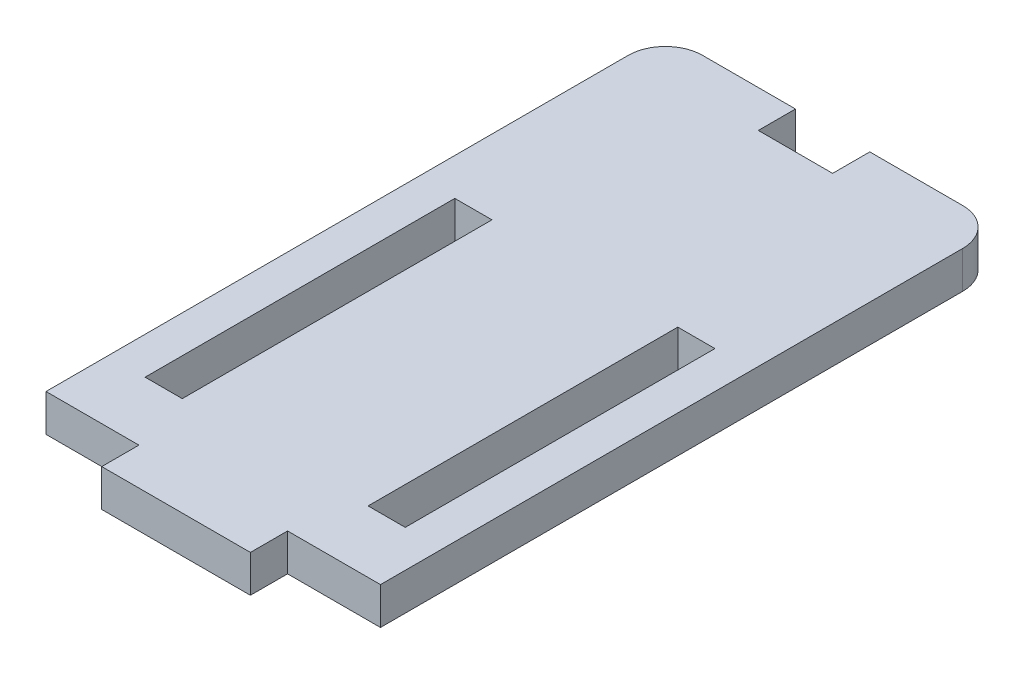
SolidWorks part; units mm, degrees
material "Acrylic (Medium-high impact)"
ref_plane "Plano frontal" through (0, 0, 0) normal (0, 0, 1) x (1, 0, 0)
ref_plane "Plano superior" through (0, 0, 0) normal (0, 1, 0) x (1, 0, 0)
ref_plane "Plano direito" through (0, 0, 0) normal (1, 0, 0) x (0, 0, -1)
sketch "Sketch1" plane through (0, 0, 0) normal (0, 1, 0) x (1, 0, 0)
  line L1 (-13.5, 25) -> (13.5, 25)
  line L2 (-13.5, 25) -> (-13.5, -25)
  line L3 (-13.5, -25) -> (13.5, -25)
  line L4 (13.5, 25) -> (13.5, -25)
  point P4 (-13.5, 0)
  point P6 (0, 25)
  dimension "D1" = 50
  dimension "D2" = 27
extrude "Boss-Extrude1" add sketch "Sketch1" along normal mid plane 3
sketch "Sketch2" plane through (0, 0, 0) normal (0, 1, 0) x (1, 0, 0)
  line L0 (-13.5, -25) -> (13.5, -25) construction
  line L1 (-6, -25) -> (6, -25)
  line L2 (-6, -25) -> (-6, -28)
  line L3 (-6, -28) -> (6, -28)
  line L4 (6, -25) -> (6, -28)
  line L5 (-13.5, 25) -> (-13.5, -25) construction
  point P6 (0, -28)
  dimension "D1" = 3
  dimension "D2" = 12
  dimension "D3" = 7.5
extrude "Boss-Extrude2" add sketch "Sketch2" along normal mid plane 3
sketch "Sketch4" plane through (0, 0, 0) normal (0, 1, 0) x (1, 0, 0)
  line L0 (-13.5, 25) -> (-13.5, -25) construction
  line L1 (-10.5, 5) -> (-7.5, 5)
  line L2 (-10.5, 5) -> (-10.5, -20)
  line L3 (-10.5, -20) -> (-7.5, -20)
  line L4 (-7.5, 5) -> (-7.5, -20)
  line L5 (0, -1.65) -> (0, 1.65) construction
  line L6 (7.5, 5) -> (7.5, -20)
  line L7 (10.5, -20) -> (7.5, -20)
  line L8 (10.5, 5) -> (10.5, -20)
  line L9 (10.5, 5) -> (7.5, 5)
  line L10 (13.5, 25) -> (-13.5, 25) construction
  dimension "D1" = 3
  dimension "D2" = 3
  dimension "D3" = 25
  dimension "D4" = 20
extrude "Cut-Extrude1" cut sketch "Sketch4" against normal through all both and the other way through all
fillet "Fillet1" radius 3 2 edges at (13.5, 0, -25) (-13.5, 0, -25)
sketch "Sketch5" plane through (0, 0, 0) normal (0, 1, 0) x (1, 0, 0)
  line L0 (10.5, 25) -> (-10.5, 25) construction
  line L1 (-3, 25) -> (3, 25)
  line L2 (-3, 25) -> (-3, 22)
  line L3 (-3, 22) -> (3, 22)
  line L4 (3, 25) -> (3, 22)
  point P6 (0, 22)
  dimension "D1" = 3
  dimension "D2" = 6
extrude "Cut-Extrude2" cut sketch "Sketch5" against normal through all both and the other way through all
